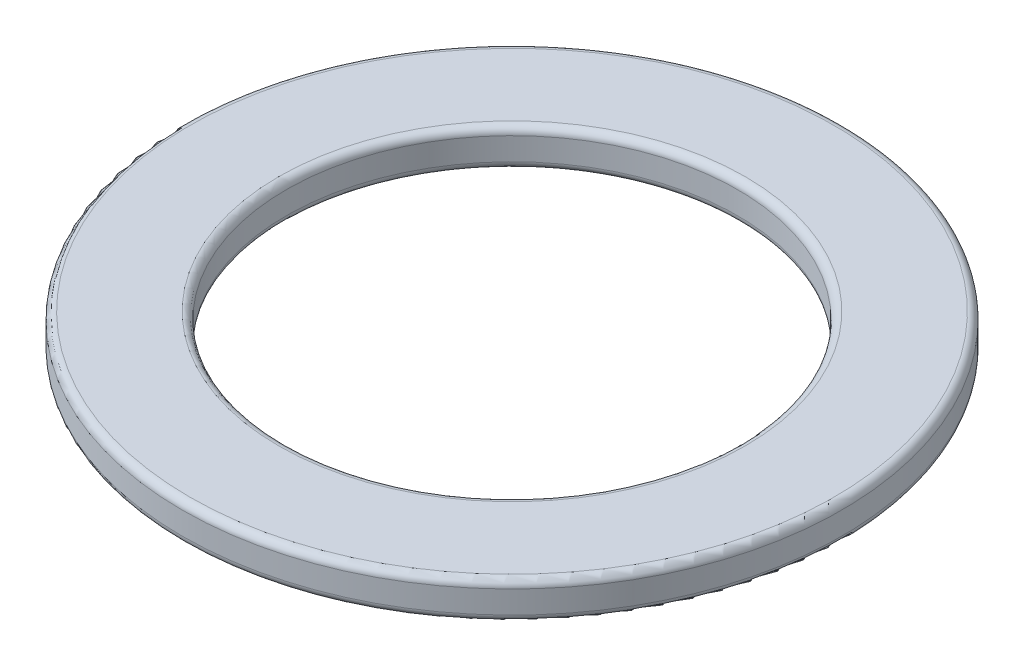
SolidWorks part; units mm, degrees
material "Cast Stainless Steel"
ref_plane "Front Plane" through (0, 0, 0) normal (0, 0, 1) x (1, 0, 0)
ref_plane "Top Plane" through (0, 0, 0) normal (0, 1, 0) x (1, 0, 0)
ref_plane "Right Plane" through (0, 0, 0) normal (1, 0, 0) x (0, 0, -1)
sketch "Sketch2" plane through (0, 0, 0) normal (0, 1, 0) x (1, 0, 0)
  circle A0 centre (0, 0) radius 3
  circle A1 centre (0, 0) radius 4.38
  dimension "D1" = 6
  dimension "D2" = 8.76
extrude "Boss-Extrude1" add sketch "Sketch2" along normal blind 0.5
fillet "Fillet1" radius 0.1 4 edges at (0, 0, 3) (0, 0, 4.38) (0, 0.5, 3) (0, 0.5, 4.38)
